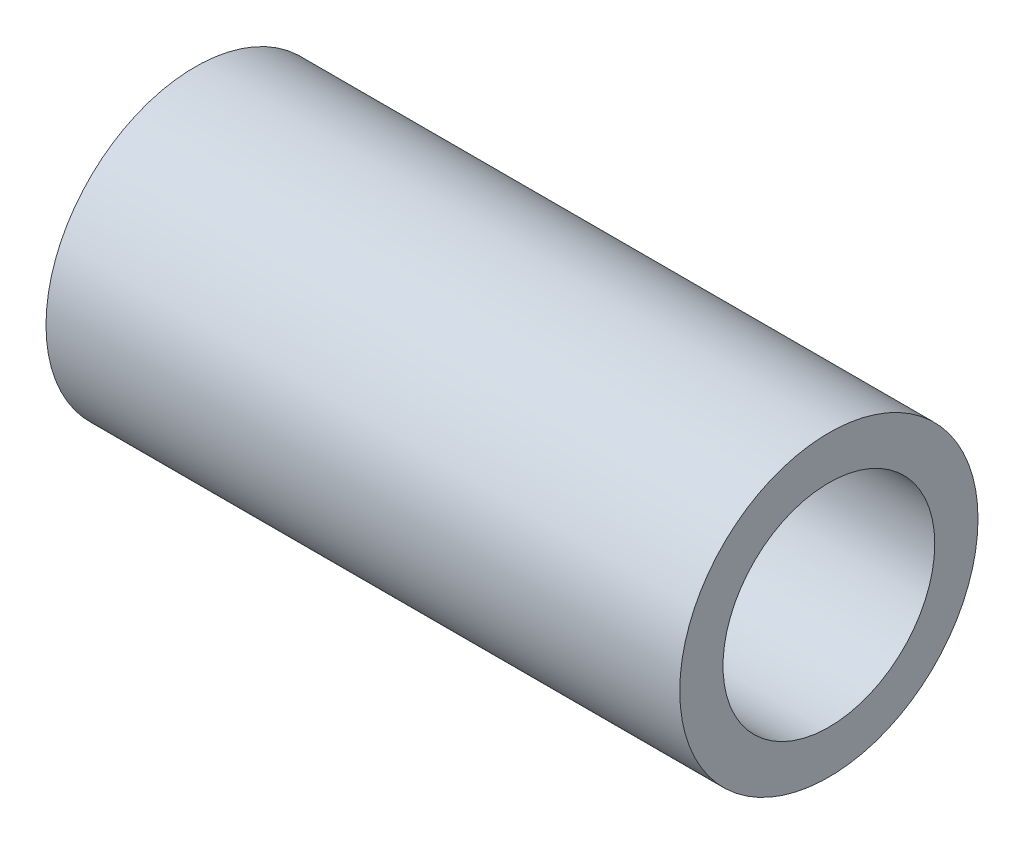
SolidWorks part; units mm, degrees
other "DetailItem1" parameters "RD2"=31.75
ref_plane "Front" through (0, 0, 0) normal (0, 0, 1) x (1, 0, 0)
ref_plane "Top" through (0, 0, 0) normal (0, 1, 0) x (1, 0, 0)
ref_plane "Right" through (0, 0, 0) normal (1, 0, 0) x (0, 0, -1)
sketch "Sketch2" plane through (0, 0, 0) normal (1, 0, 0) x (0, 0, -1)
  circle A0 centre (0, 0) radius 12.7
  circle A1 centre (0, 0) radius 11.2141
  dimension "D1" = 25.4
  dimension "D2" = 22.4282
extrude "Extrude1" add sketch "Sketch2" along normal blind 28.575
cosmetic thread "Cosmetic Thread1" parameters "D1"=15.24, "D2"=23.8125
sketch "Sketch3" plane through (28.575, 0, 0) normal (1, 0, 0) x (0, 0, -1)
  circle A0 centre (0, 0) radius 9.017
  circle A1 centre (0, 0) radius 12.7 construction
  circle A2 centre (0, 0) radius 12.7
  dimension "D1" = 18.034
extrude "Extrude2" add sketch "Sketch3" along normal blind 25.4
sketch "Sketch4" plane through (28.575, 0, 0) normal (-1, 0, 0) x (0, 0, 1)
  circle A0 centre (0, 0) radius 9.017 construction
  circle A1 centre (0, 0) radius 11.2141
  circle A2 centre (0, 0) radius 11.2141
  circle A3 centre (0, 0) radius 9.017
  dimension "D1" = 0
extrude "Cut-Extrude3" cut sketch "Sketch4" against normal offset from surface (3.175 mm away) 31.75 up to face at (0, 0, -12.7)
